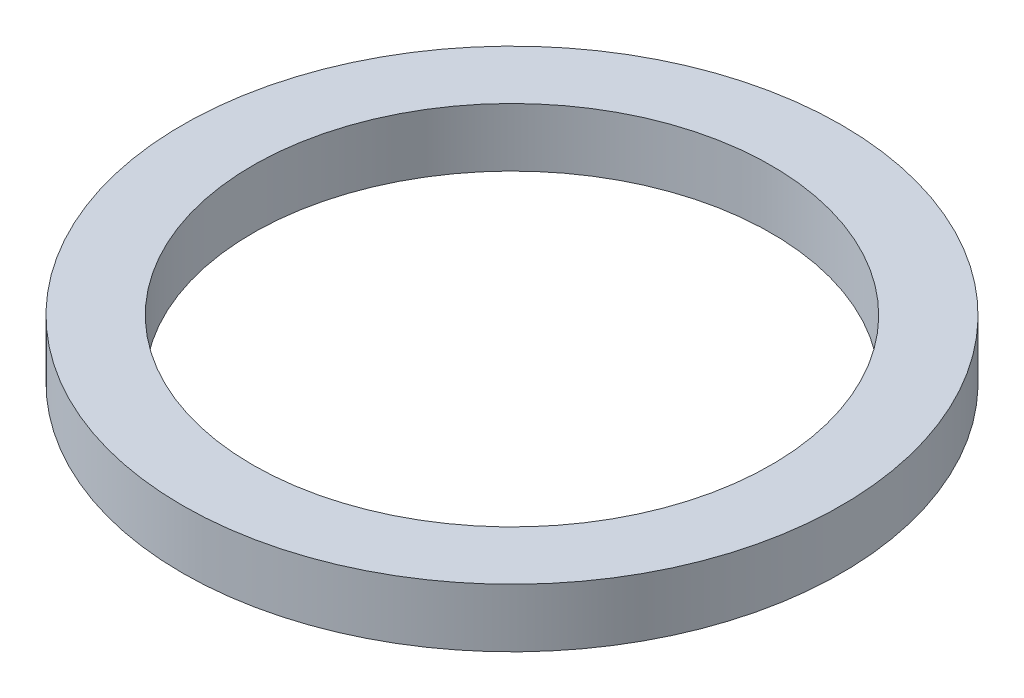
SolidWorks part; units mm, degrees
ref_plane "Front Plane" through (0, 0, 0) normal (0, 0, 1) x (1, 0, 0)
ref_plane "Top Plane" through (0, 0, 0) normal (0, 1, 0) x (1, 0, 0)
ref_plane "Right Plane" through (0, 0, 0) normal (1, 0, 0) x (0, 0, -1)
sketch "Sketch1" plane through (0, 0, 0) normal (0, 1, 0) x (1, 0, 0)
  circle A0 centre (0, 0) radius 44.3
  circle A1 centre (0, 0) radius 56.3
  dimension "D1" = 88.6
  dimension "D2" = 112.6
extrude "Boss-Extrude1" add sketch "Sketch1" along normal blind 10
